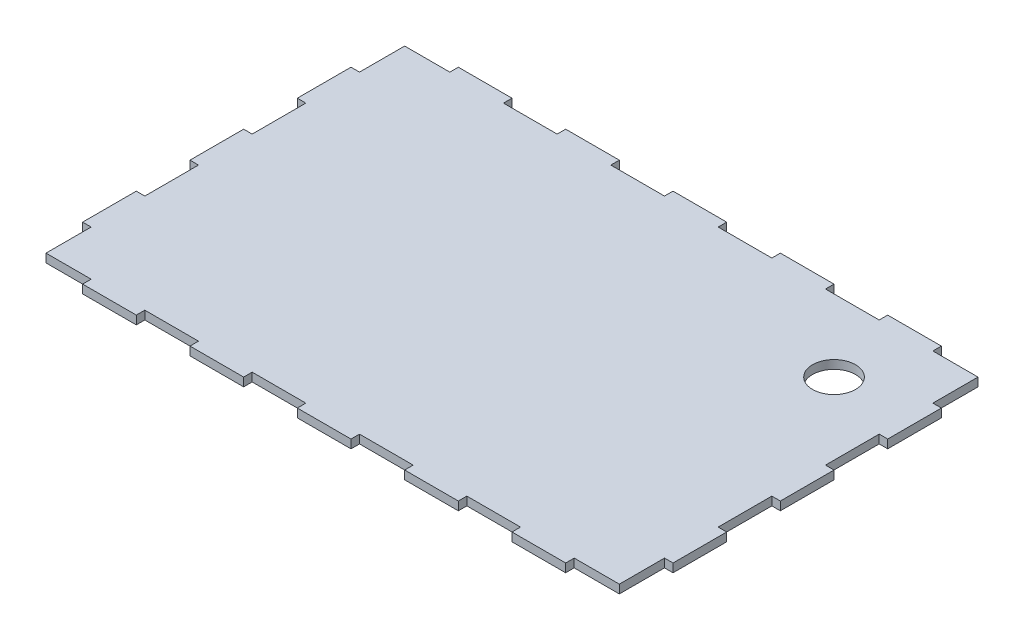
SolidWorks part; units mm, degrees
material "Acrylic (Medium-high impact)"
ref_plane "Front Plane" through (0, 0, 0) normal (0, 0, 1) x (1, 0, 0)
ref_plane "Top Plane" through (0, 0, 0) normal (0, 1, 0) x (1, 0, 0)
ref_plane "Right Plane" through (0, 0, 0) normal (1, 0, 0) x (0, 0, -1)
sketch "Sketch48" plane through (0, 0, 0) normal (0, -1, 0) x (1, 0, 0)
  line L4 (-110, 738.1019) -> (110, 738.1019)
  line L5 (-110, 738.1019) -> (-110, 598.1019)
  line L6 (-110, 598.1019) -> (110, 598.1019)
  line L7 (110, 738.1019) -> (110, 598.1019)
extrude "Boss-Extrude12" add sketch "Sketch48" along normal blind 3.175 separate body
sketch "Sketch49" plane through (0, -3.175, 0) normal (0, -1, 0) x (-1, 0, 0)
  line L0 (70, -738.1019) -> (70, -734.9269)
  line L2 (-110, -738.1019) -> (110, -738.1019) construction
  line L3 (70, -738.1019) -> (50, -738.1019)
  line L8 (50, -738.1019) -> (50, -734.9269)
  line L9 (110, -738.1019) -> (90, -738.1019)
  line L12 (90, -738.1019) -> (90, -734.9269)
  line L13 (70, -734.9269) -> (50, -734.9269)
  line L14 (30, -738.1019) -> (30, -734.9269)
  line L15 (30, -738.1019) -> (10, -738.1019)
  line L16 (10, -738.1019) -> (10, -734.9269)
  line L17 (30, -734.9269) -> (10, -734.9269)
  line L18 (-10, -738.1019) -> (-10, -734.9269)
  line L19 (-10, -738.1019) -> (-30, -738.1019)
  line L20 (-30, -738.1019) -> (-30, -734.9269)
  line L21 (-10, -734.9269) -> (-30, -734.9269)
  line L22 (-50, -738.1019) -> (-50, -734.9269)
  line L23 (-50, -738.1019) -> (-70, -738.1019)
  line L24 (-70, -738.1019) -> (-70, -734.9269)
  line L25 (-50, -734.9269) -> (-70, -734.9269)
  line L26 (-90, -738.1019) -> (-90, -734.9269)
  line L27 (-90, -738.1019) -> (-110, -738.1019)
  line L30 (70, -598.1019) -> (70, -601.2769)
  line L31 (110, -598.1019) -> (-110, -598.1019) construction
  line L32 (70, -598.1019) -> (50, -598.1019)
  line L33 (50, -598.1019) -> (50, -601.2769)
  line L34 (110, -598.1019) -> (90, -598.1019)
  line L37 (90, -598.1019) -> (90, -601.2769)
  line L38 (70, -601.2769) -> (50, -601.2769)
  line L39 (30, -598.1019) -> (30, -601.2769)
  line L40 (30, -598.1019) -> (10, -598.1019)
  line L41 (10, -598.1019) -> (10, -601.2769)
  line L42 (30, -601.2769) -> (10, -601.2769)
  line L43 (-10, -598.1019) -> (-10, -601.2769)
  line L44 (-10, -598.1019) -> (-30, -598.1019)
  line L45 (-30, -598.1019) -> (-30, -601.2769)
  line L46 (-10, -601.2769) -> (-30, -601.2769)
  line L47 (-50, -598.1019) -> (-50, -601.2769)
  line L48 (-50, -598.1019) -> (-70, -598.1019)
  line L49 (-70, -598.1019) -> (-70, -601.2769)
  line L50 (-50, -601.2769) -> (-70, -601.2769)
  line L51 (-90, -598.1019) -> (-90, -601.2769)
  line L52 (-90, -598.1019) -> (-110, -598.1019)
  line L55 (110, -738.1019) -> (110, -718.1019)
  line L56 (110, -738.1019) -> (110, -598.1019) construction
  line L57 (110, -718.1019) -> (106.825, -718.1019)
  line L58 (106.825, -718.1019) -> (106.825, -734.9269)
  line L59 (106.825, -734.9269) -> (90, -734.9269)
  line L60 (110, -598.1019) -> (110, -618.1019)
  line L61 (110, -618.1019) -> (106.825, -618.1019)
  line L62 (106.825, -618.1019) -> (106.825, -601.2769)
  line L63 (106.825, -601.2769) -> (90, -601.2769)
  line L64 (-110, -738.1019) -> (-110, -718.1019)
  line L65 (-110, -598.1019) -> (-110, -738.1019) construction
  line L66 (-110, -718.1019) -> (-106.825, -718.1019)
  line L67 (-106.825, -718.1019) -> (-106.825, -734.9269)
  line L68 (-106.825, -734.9269) -> (-90, -734.9269)
  line L69 (-110, -738.1019) -> (-110, -734.9269) [skipped]
  line L70 (-110, -598.1019) -> (-110, -618.1019)
  line L71 (-110, -618.1019) -> (-106.825, -618.1019)
  line L72 (-106.825, -618.1019) -> (-106.825, -601.2769)
  line L73 (-106.825, -601.2769) -> (-90, -601.2769)
  line L74 (-110, -598.1019) -> (-110, -601.2769) [skipped]
  line L75 (110, -658.1019) -> (110, -638.1019)
  line L76 (110, -658.1019) -> (106.825, -658.1019)
  line L77 (106.825, -658.1019) -> (106.825, -638.1019)
  line L78 (110, -698.1019) -> (106.825, -698.1019)
  line L79 (110, -698.1019) -> (110, -678.1019)
  line L80 (110, -678.1019) -> (106.825, -678.1019)
  line L81 (106.825, -698.1019) -> (106.825, -678.1019)
  line L82 (110, -638.1019) -> (106.825, -638.1019)
  line L83 (-110, -658.1019) -> (-110, -638.1019)
  line L84 (-110, -658.1019) -> (-106.825, -658.1019)
  line L85 (-106.825, -658.1019) -> (-106.825, -638.1019)
  line L86 (-110, -698.1019) -> (-106.825, -698.1019)
  line L87 (-110, -698.1019) -> (-110, -678.1019)
  line L88 (-110, -678.1019) -> (-106.825, -678.1019)
  line L89 (-106.825, -698.1019) -> (-106.825, -678.1019)
  line L90 (-110, -638.1019) -> (-106.825, -638.1019)
  circle A1 centre (-80, -628.1019) radius 8
  dimension "D1" = 6
  dimension "D2" = 6
  dimension "D3" = 2
  dimension "D4" = 2
extrude "Cut-Extrude24" cut sketch "Sketch49" against normal blind 3.175
